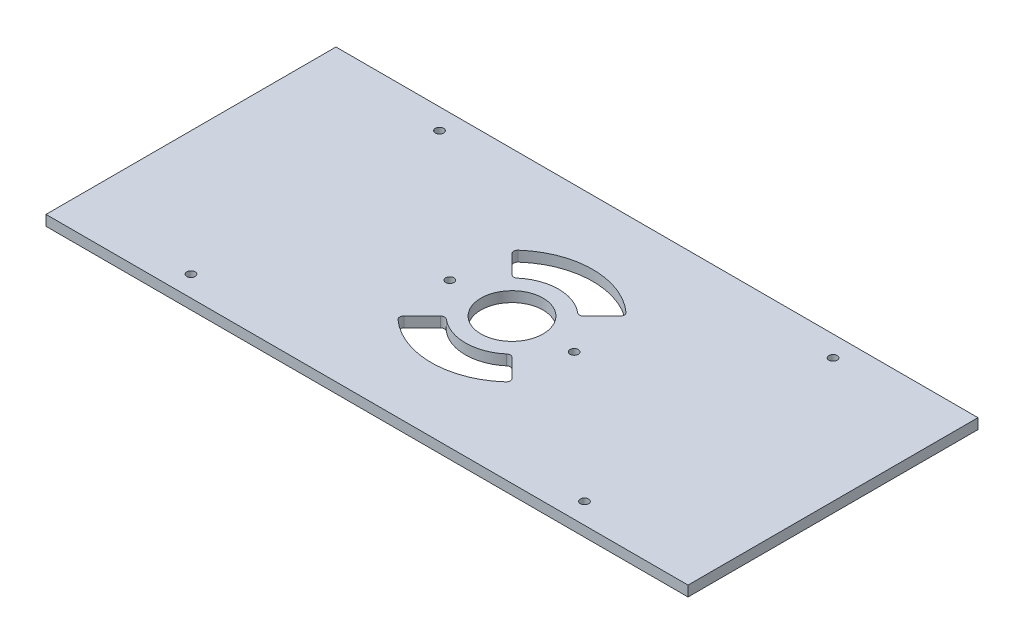
SolidWorks part; units mm, degrees
ref_plane "前视基准面" through (0, 0, 0) normal (0, 0, 1) x (1, 0, 0)
ref_plane "上视基准面" through (0, 0, 0) normal (0, 1, 0) x (1, 0, 0)
ref_plane "右视基准面" through (0, 0, 0) normal (1, 0, 0) x (0, 0, -1)
sketch "Sketch2" plane through (0, 0, 0) normal (0, 1, 0) x (1, 0, 0)
  line L1 (-155, 70) -> (155, 70)
  line L2 (-155, 70) -> (-155, -70)
  line L3 (-155, -70) -> (155, -70)
  line L4 (155, 70) -> (155, -70)
  line L5 (-155, 70) -> (155, -70) construction
  line L6 (-155, -70) -> (155, 70) construction
  point P0 (0, 0)
  dimension "D1" = 310
  dimension "D2" = 140
extrude "Boss-Extrude1" add sketch "Sketch2" along normal blind 5
sketch "Sketch3" plane through (0, 5, 0) normal (0, 1, 0) x (1, 0, 0)
  line L0 (155, -70) -> (155, 70) construction
  line L2 (155, 70) -> (-155, 70) construction
  circle A0 centre (0, 0) radius 15
  dimension "D1" = 30
  dimension "D3" = 70
  dimension "D2" = 155
extrude "Cut-Extrude1" cut sketch "Sketch3" against normal through all
sketch "Sketch5" plane through (0, 5, 0) normal (0, 1, 0) x (1, 0, 0)
  line L0 (-155, 0) -> (155, 0) construction
  line L1 (-155, 70) -> (-155, -70) construction
  line L2 (155, -70) -> (155, 70) construction
  line L3 (-155, 60) -> (155, 60) construction
  line L4 (155, 70) -> (-155, 70) construction
  line L5 (0, 0) -> (0, 70) construction
  circle A0 centre (-95, 60) radius 2
  circle A1 centre (95, 60) radius 2
  circle A2 centre (95, -60) radius 2
  circle A3 centre (-95, -60) radius 2
  dimension "D2" = 60
  dimension "D3" = 4
  dimension "D1" = 10
extrude "Cut-Extrude2" cut sketch "Sketch5" against normal through all
sketch "Sketch6" plane through (0, 5, 0) normal (0, 1, 0) x (1, 0, 0)
  line L0 (0, 0) -> (27.5772, 27.5772)
  line L1 (0, 0) -> (39, 0) construction
  line L2 (0, 0) -> (27.5772, -27.5772)
  line L3 (0, 0) -> (-27.5772, -27.5772)
  line L4 (0, 0) -> (-27.5772, 27.5772)
  circle A0 centre (0, 0) radius 39
  circle A1 centre (0, 0) radius 22.5
  point P12 (0, 0)
  dimension "D1" = 78
  dimension "D2" = 45
  dimension "D3" = 45
  dimension "D4" = 4
extrude "Cut-Extrude3" cut sketch "Sketch6" against normal blind 10 contours A1 L3 A0 L2 | A1 L0 A0 L4
fillet "Fillet1" radius 2 8 edges at (15.9099, 2.5, 15.9099) (27.5772, 2.5, 27.5772) (-27.5772, 2.5, 27.5772) (-15.9099, 2.5, 15.9099) (-15.9099, 2.5, -15.9099) (27.5772, 2.5, -27.5772) (15.9099, 2.5, -15.9099) (-27.5772, 2.5, -27.5772)
sketch "Sketch7" plane through (0, 5, 0) normal (0, 1, 0) x (1, 0, 0)
  line L0 (-30, 0) -> (30, 0) construction
  circle A0 centre (-30, 0) radius 2
  circle A1 centre (30, 0) radius 2
  point P4 (0, 0)
  dimension "D2" = 4
  dimension "D3" = 4
  dimension "D1" = 60
extrude "Cut-Extrude4" cut sketch "Sketch7" against normal through all
